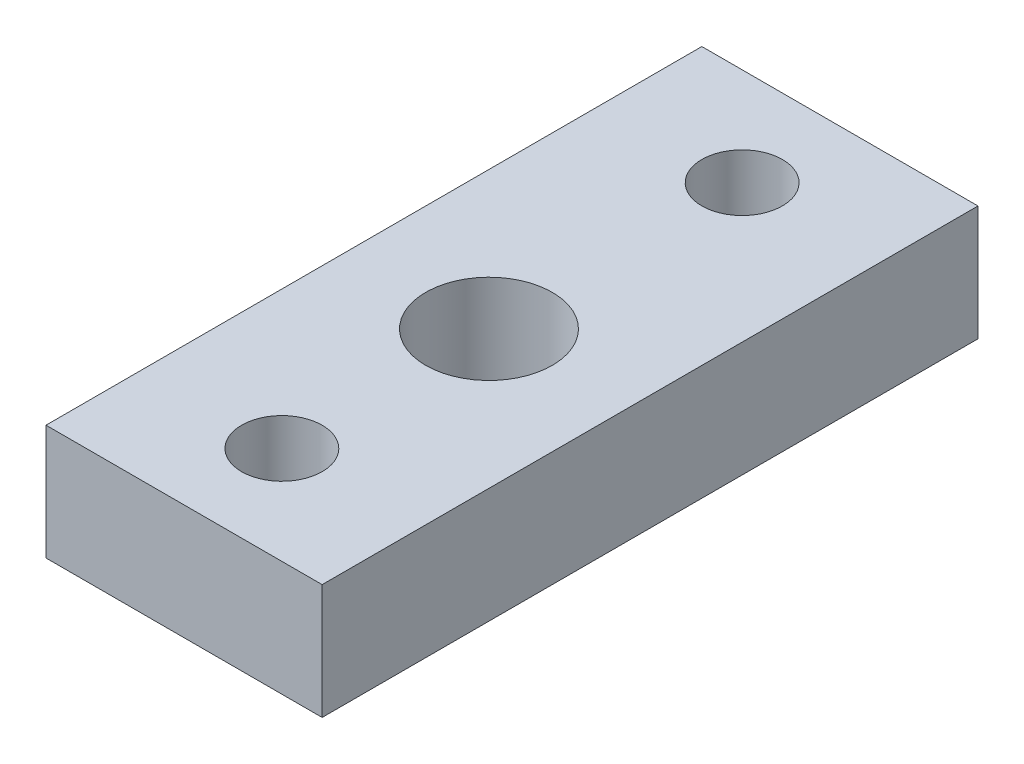
SolidWorks part; units mm, degrees
material "ABS PC"
ref_plane "Front Plane" through (0, 0, 0) normal (0, 0, 1) x (1, 0, 0)
ref_plane "Top Plane" through (0, 0, 0) normal (0, 1, 0) x (1, 0, 0)
ref_plane "Right Plane" through (0, 0, 0) normal (1, 0, 0) x (0, 0, -1)
sketch "Sketch1" plane through (0, 0, 0) normal (0, 1, 0) x (1, 0, 0)
  line L0 (0, 0) -> (0, 28.5)
  line L1 (0, 0) -> (12, 0)
  line L2 (0, 28.5) -> (12, 28.5)
  line L3 (12, 0) -> (12, 28.5)
  circle A0 centre (6, 24.25) radius 1.75
  circle A1 centre (6, 4.25) radius 1.75
  circle A2 centre (6, 13.25) radius 2.75
  dimension "D3" = 3.5
  dimension "D4" = 4.25
  dimension "D7" = 5.5
  dimension "D8" = 9
  dimension "D1" = 12
  dimension "D2" = 28.5
  dimension "D5" = 4.25
  dimension "D6" = 6
extrude "Boss-Extrude1" add sketch "Sketch1" along normal blind 5
sketch "Sketch2" plane through (0, 5, 0) normal (0, 1, 0) x (1, 0, 0)
  circle A0 centre (6, 13.25) radius 4.45
  circle A1 centre (6, 13.25) radius 2.75 construction
  dimension "D1" = 8.9
